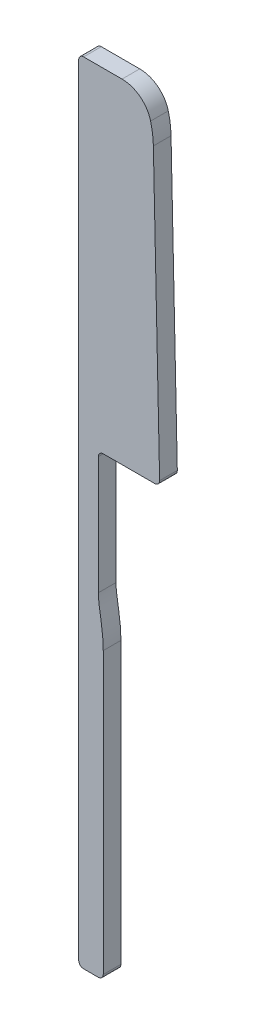
SolidWorks part; units mm, degrees
material "1060 Alloy"
ref_plane "Front Plane" through (0, 0, 0) normal (0, 0, 1) x (1, 0, 0)
ref_plane "Top Plane" through (0, 0, 0) normal (0, 1, 0) x (1, 0, 0)
ref_plane "Right Plane" through (0, 0, 0) normal (1, 0, 0) x (0, 0, -1)
sketch "Sketch1" plane through (0, 0, 0) normal (0, 0, 1) x (1, 0, 0)
  line L0 (0, 0) -> (0, 83.5) construction
  line L1 (0, 83.5) -> (18.25, 83.5) construction
  line L2 (18.25, 83.5) -> (18.25, 0) construction
  line L3 (18.25, 0) -> (0, 0) construction
  line L4 (0, 4.5) -> (0, 6.5)
  line L5 (0, 6.5) -> (6, 6.5)
  line L6 (6, 6.5) -> (6, 10.5)
  line L7 (6, 10.5) -> (10, 14.5)
  line L8 (10, 14.5) -> (10, 83.5)
  line L9 (18.25, 49.5) -> (17.602, 79.1992)
  line L10 (18.25, 49.5) -> (12, 49.5)
  line L11 (12, 49.5) -> (12, 37)
  line L12 (12.5, 32.15) -> (12.5, 2.89)
  line L13 (12, 35.4908) -> (12, 38.5096) construction
  line L14 (12.5, 30.5478) -> (12.5, 33.7533) construction
  line L15 (10, 83.5) -> (16.4, 83.5)
  arc A0 (17.602, 79.1992) -> (16.4, 83.5) centre (8.6041, 79.0029) ccw
  arc A1 (12.5, 2.89) -> (9.61, 0) centre (9.61, 2.89) cw
  arc A2 (9.61, 0) -> (0, 4.5) centre (9.61, 12.5113) cw
  spline S0 degree 3 poles (12, 37) (12, 35.7422) (12.5, 34.1535) (12.5, 32.15) knots 0 0 0 0 1 1 1 1
  point P3 (0, 4.5)
  point P6 (0, 6.5)
  point P7 (16.4, 83.5)
  point P8 (18.25, 49.5)
  dimension "D12" = 9
  dimension "D1" = 83.5
  dimension "D2" = 18.25
  dimension "D3" = 4.5
  dimension "D4" = 2
  dimension "D5" = 34
  dimension "D6" = 1.85
  dimension "D7" = 6
  dimension "D8" = 4
  dimension "D9" = 45
  dimension "D10" = 1.25
  dimension "D11" = 4
  dimension "D13" = 6.25
  dimension "D14" = 12.5
  dimension "D15" = 29.26
  dimension "D16" = 2.5
  dimension "D17" = 4.85
extrude "Boss-Extrude1" add sketch "Sketch1" along normal blind 1.8
fillet "Fillet1" radius 0.5 8 edges at (10, 83.5, 0.9) (0, 4.5, 0.9) (0, 6.5, 0.9) (6, 6.5, 0.9) (10, 14.5, 0.9) (6, 10.5, 0.9) (12, 49.5, 0.9) (18.25, 49.5, 0.9)
sketch "Sketch2" plane through (0, 0, 0) normal (0, 0, 1) x (1, 0, 0)
  line L0 (7, -2.4996) -> (7, 0.5004)
  line L1 (7, 0.5004) -> (11, 0.5004)
  line L2 (11, 0.5004) -> (11.824, -1.5783)
  line L3 (12.5, 2.89) -> (12.5, 32.15) construction
  arc A0 (7, -2.4996) -> (11.824, -1.5783) centre (9.5, -2.4996) ccw
  arc A1 (0.1208, 4.3573) -> (9.61, 0) centre (9.61, 12.5113) ccw construction
  circle A2 centre (9.5, -2.4996) radius 1.75
  dimension "D1" = 5
  dimension "D3" = 3
  dimension "D2" = 3
  dimension "D4" = 4
extrude "Boss-Extrude3" add sketch "Sketch2" along normal blind 1.8
sketch "Sketch5" plane through (0, 0, 0) normal (0, 0, 1) x (1, 0, 0)
  line L0 (10, 29.5424) -> (10, 3.09)
  line L1 (10, 83) -> (10, 14.7071) construction
  line L2 (10, 3.09) -> (19.8682, 3.09)
  line L3 (19.8682, 3.09) -> (19.8682, -10.0136)
  line L4 (19.8682, -10.0136) -> (-11.1959, -10.0136)
  line L5 (-11.1959, -10.0136) -> (-11.1959, 29.5424)
  line L6 (-11.1959, 29.5424) -> (10, 29.5424)
  dimension "D1" = 0.2
extrude "Cut-Extrude2" cut sketch "Sketch5" along normal blind 1.8
fillet "Fillet2" radius 0.5 2 edges at (12.5, 3.09, 0.9) (10, 3.09, 0.9)
fillet "Fillet3" radius 3 1 edges at (16.4, 83.5, 0.9)
